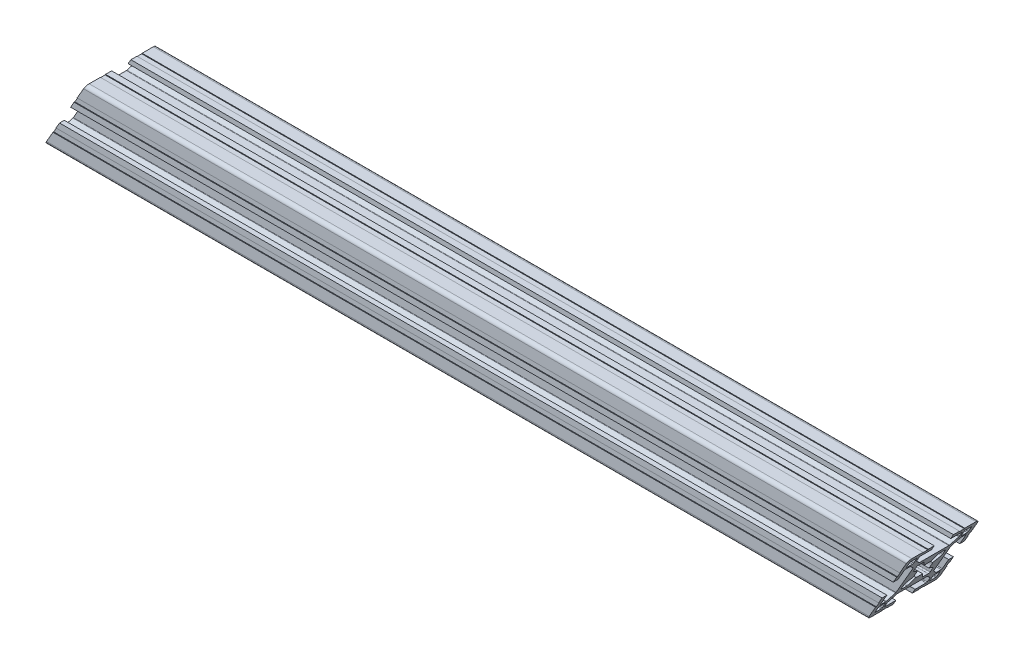
SolidWorks part; units mm, degrees
material "6063-T5"
ref_plane "Plano frontal" through (0, 0, 0) normal (0, 0, 1) x (1, 0, 0)
ref_plane "Plano superior" through (0, 0, 0) normal (0, 1, 0) x (1, 0, 0)
ref_plane "Plano direito" through (0, 0, 0) normal (1, 0, 0) x (0, 0, -1)
sketch "Esboço1" plane through (0, 0, 0) normal (0, 0, 1) x (1, 0, 0)
  line L0 (0, 0) -> (363.73, 0)
  dimension "D1" = 363.73
other "Quadrado PF30-11 - PERFIL 3030 CENTRO M8(1)"
ref_plane "Plano1" through (0, 0, 0) normal (1, 0, 0) x (0, 1, 0)
sketch "Sketch1" plane through (0, 0, 0) normal (1, 0, 0) x (0, 1, 0)
  line L0 (-6.1, -3.4254) -> (-6.1, -5.6)
  line L1 (-5.6, -6.1) -> (-3.4254, -6.1)
  line L2 (3.4254, -6.1) -> (5.6, -6.1)
  line L3 (6.1, -5.6) -> (6.1, -3.4254)
  line L4 (6.1, 3.4254) -> (6.1, 5.6)
  line L5 (5.6, 6.1) -> (3.4254, 6.1)
  line L6 (-3.4254, 6.1) -> (-5.6, 6.1)
  line L7 (-6.1, 5.6) -> (-6.1, 3.4254)
  line L8 (15, 6.6) -> (14.7, 6.6)
  line L9 (5.85, -2.9924) -> (3.097, -1.403)
  line L10 (10, 12.7) -> (10, 10.3)
  line L11 (13, -12.7) -> (13, -10.3)
  line L12 (-10.3, -10) -> (-12.7, -10)
  line L13 (-13, 12.7) -> (-13, 10.3)
  line L14 (3.097, 1.403) -> (5.85, 2.9924)
  line L15 (2.9924, 5.85) -> (1.403, 3.097)
  line L16 (-1.403, 3.097) -> (-2.9924, 5.85)
  line L17 (-5.85, 2.9924) -> (-3.097, 1.403)
  line L18 (-3.097, -1.403) -> (-5.85, -2.9924)
  line L19 (-2.9924, -5.85) -> (-1.403, -3.097)
  line L20 (1.403, -3.097) -> (2.9924, -5.85)
  line L21 (10.3, 10) -> (12.7, 10)
  line L22 (13, 10.3) -> (13, 12.7)
  line L23 (12.7, 13) -> (10.3, 13)
  line L24 (12.7, -10) -> (10.3, -10)
  line L25 (10, -10.3) -> (10, -12.7)
  line L26 (10.3, -13) -> (12.7, -13)
  line L27 (-13, -10.3) -> (-13, -12.7)
  line L28 (-12.7, -13) -> (-10.3, -13)
  line L29 (-10, -12.7) -> (-10, -10.3)
  line L30 (-12.7, 10) -> (-10.3, 10)
  line L31 (-10, 10.3) -> (-10, 12.7)
  line L32 (-10.3, 13) -> (-12.7, 13)
  line L33 (15, 4.05) -> (15, 6.6)
  line L34 (13, 4.05) -> (15, 4.05)
  line L35 (13, 8.7) -> (13, 4.05)
  line L36 (10.6799, 9) -> (12.7, 9)
  line L37 (7.9879, 6.4322) -> (10.4678, 8.9121)
  line L38 (7.9, -6.2201) -> (7.9, 6.2201)
  line L39 (10.4678, -8.9121) -> (7.9879, -6.4322)
  line L40 (12.7, -9) -> (10.6799, -9)
  line L41 (13, -4.05) -> (13, -8.7)
  line L42 (15, -4.05) -> (13, -4.05)
  line L43 (15, -6.6) -> (15, -4.05)
  line L44 (14.7, -6.6) -> (15, -6.6)
  line L45 (14.7, -8.8) -> (14.7, -6.6)
  line L46 (15, -8.8) -> (14.7, -8.8)
  line L47 (15, -13.5) -> (15, -8.8)
  line L48 (8.8, -15) -> (13.5, -15)
  line L49 (8.8, -14.7) -> (8.8, -15)
  line L50 (6.6, -14.7) -> (8.8, -14.7)
  line L51 (6.6, -15) -> (6.6, -14.7)
  line L52 (4.05, -15) -> (6.6, -15)
  line L53 (4.05, -13) -> (4.05, -15)
  line L54 (8.7, -13) -> (4.05, -13)
  line L55 (9, -10.6799) -> (9, -12.7)
  line L56 (6.4322, -7.9879) -> (8.9121, -10.4678)
  line L57 (-6.2201, -7.9) -> (6.2201, -7.9)
  line L58 (-8.9121, -10.4678) -> (-6.4322, -7.9879)
  line L59 (-9, -12.7) -> (-9, -10.6799)
  line L60 (-4.05, -13) -> (-8.7, -13)
  line L61 (-4.05, -15) -> (-4.05, -13)
  line L62 (-6.6, -15) -> (-4.05, -15)
  line L63 (-6.6, -14.7) -> (-6.6, -15)
  line L64 (-8.8, -14.7) -> (-6.6, -14.7)
  line L65 (-8.8, -15) -> (-8.8, -14.7)
  line L66 (-13.5, -15) -> (-8.8, -15)
  line L67 (-15, -8.8) -> (-15, -13.5)
  line L68 (-14.7, -8.8) -> (-15, -8.8)
  line L69 (-14.7, -6.6) -> (-14.7, -8.8)
  line L70 (-15, -6.6) -> (-14.7, -6.6)
  line L71 (-15, -4.05) -> (-15, -6.6)
  line L72 (-13, -4.05) -> (-15, -4.05)
  line L73 (-13, -8.7) -> (-13, -4.05)
  line L74 (-10.6799, -9) -> (-12.7, -9)
  line L75 (-7.9879, -6.4322) -> (-10.4678, -8.9121)
  line L76 (-7.9, 6.2201) -> (-7.9, -6.2201)
  line L77 (-10.4678, 8.9121) -> (-7.9879, 6.4322)
  line L78 (-12.7, 9) -> (-10.6799, 9)
  line L79 (-13, 4.05) -> (-13, 8.7)
  line L80 (-15, 4.05) -> (-13, 4.05)
  line L81 (-15, 6.6) -> (-15, 4.05)
  line L82 (-14.7, 6.6) -> (-15, 6.6)
  line L83 (-14.7, 8.8) -> (-14.7, 6.6)
  line L84 (-15, 8.8) -> (-14.7, 8.8)
  line L85 (-15, 13.5) -> (-15, 8.8)
  line L86 (-8.8, 15) -> (-13.5, 15)
  line L87 (-8.8, 14.7) -> (-8.8, 15)
  line L88 (-6.6, 14.7) -> (-8.8, 14.7)
  line L89 (-6.6, 15) -> (-6.6, 14.7)
  line L90 (-4.05, 15) -> (-6.6, 15)
  line L91 (-4.05, 13) -> (-4.05, 15)
  line L92 (-8.7, 13) -> (-4.05, 13)
  line L93 (-9, 10.6799) -> (-9, 12.7)
  line L94 (-6.4322, 7.9879) -> (-8.9121, 10.4678)
  line L95 (6.2201, 7.9) -> (-6.2201, 7.9)
  line L96 (8.9121, 10.4678) -> (6.4322, 7.9879)
  line L97 (9, 12.7) -> (9, 10.6799)
  line L98 (4.05, 13) -> (8.7, 13)
  line L99 (4.05, 15) -> (4.05, 13)
  line L100 (6.6, 15) -> (4.05, 15)
  line L101 (6.6, 14.7) -> (6.6, 15)
  line L102 (8.8, 14.7) -> (6.6, 14.7)
  line L103 (8.8, 15) -> (8.8, 14.7)
  line L104 (13.5, 15) -> (8.8, 15)
  line L105 (15, 8.8) -> (15, 13.5)
  line L106 (14.7, 8.8) -> (15, 8.8)
  line L107 (14.7, 6.6) -> (14.7, 8.8)
  arc A0 (-5.85, -2.9924) -> (-6.1, -3.4254) centre (-5.6, -3.4254) ccw
  arc A1 (-6.1, -5.6) -> (-5.6, -6.1) centre (-5.6, -5.6) ccw
  arc A2 (-3.4254, -6.1) -> (-2.9924, -5.85) centre (-3.4254, -5.6) ccw
  arc A3 (2.9924, -5.85) -> (3.4254, -6.1) centre (3.4254, -5.6) ccw
  arc A4 (5.6, -6.1) -> (6.1, -5.6) centre (5.6, -5.6) ccw
  arc A5 (6.1, -3.4254) -> (5.85, -2.9924) centre (5.6, -3.4254) ccw
  arc A6 (5.85, 2.9924) -> (6.1, 3.4254) centre (5.6, 3.4254) ccw
  arc A7 (6.1, 5.6) -> (5.6, 6.1) centre (5.6, 5.6) ccw
  arc A8 (3.4254, 6.1) -> (2.9924, 5.85) centre (3.4254, 5.6) ccw
  arc A9 (-2.9924, 5.85) -> (-3.4254, 6.1) centre (-3.4254, 5.6) ccw
  arc A10 (-5.6, 6.1) -> (-6.1, 5.6) centre (-5.6, 5.6) ccw
  arc A11 (-6.1, 3.4254) -> (-5.85, 2.9924) centre (-5.6, 3.4254) ccw
  arc A12 (3.097, -1.403) -> (3.097, 1.403) centre (0, 0) ccw
  arc A13 (1.403, 3.097) -> (-1.403, 3.097) centre (0, 0) ccw
  arc A14 (-3.097, 1.403) -> (-3.097, -1.403) centre (0, 0) ccw
  arc A15 (-1.403, -3.097) -> (1.403, -3.097) centre (0, 0) ccw
  arc A16 (10, 10.3) -> (10.3, 10) centre (10.3, 10.3) ccw
  arc A17 (12.7, 10) -> (13, 10.3) centre (12.7, 10.3) ccw
  arc A18 (13, 12.7) -> (12.7, 13) centre (12.7, 12.7) ccw
  arc A19 (10.3, 13) -> (10, 12.7) centre (10.3, 12.7) ccw
  arc A20 (13, -10.3) -> (12.7, -10) centre (12.7, -10.3) ccw
  arc A21 (10.3, -10) -> (10, -10.3) centre (10.3, -10.3) ccw
  arc A22 (10, -12.7) -> (10.3, -13) centre (10.3, -12.7) ccw
  arc A23 (12.7, -13) -> (13, -12.7) centre (12.7, -12.7) ccw
  arc A24 (-12.7, -10) -> (-13, -10.3) centre (-12.7, -10.3) ccw
  arc A25 (-13, -12.7) -> (-12.7, -13) centre (-12.7, -12.7) ccw
  arc A26 (-10.3, -13) -> (-10, -12.7) centre (-10.3, -12.7) ccw
  arc A27 (-10, -10.3) -> (-10.3, -10) centre (-10.3, -10.3) ccw
  arc A28 (-13, 10.3) -> (-12.7, 10) centre (-12.7, 10.3) ccw
  arc A29 (-10.3, 10) -> (-10, 10.3) centre (-10.3, 10.3) ccw
  arc A30 (-10, 12.7) -> (-10.3, 13) centre (-10.3, 12.7) ccw
  arc A31 (-12.7, 13) -> (-13, 12.7) centre (-12.7, 12.7) ccw
  arc A32 (13, 8.7) -> (12.7, 9) centre (12.7, 8.7) ccw
  arc A33 (10.6799, 9) -> (10.4678, 8.9121) centre (10.6799, 8.7) ccw
  arc A34 (7.9879, 6.4322) -> (7.9, 6.2201) centre (8.2, 6.2201) ccw
  arc A35 (7.9, -6.2201) -> (7.9879, -6.4322) centre (8.2, -6.2201) ccw
  arc A36 (10.4678, -8.9121) -> (10.6799, -9) centre (10.6799, -8.7) ccw
  arc A37 (12.7, -9) -> (13, -8.7) centre (12.7, -8.7) ccw
  arc A38 (13.5, -15) -> (15, -13.5) centre (13.5, -13.5) ccw
  arc A39 (8.7, -13) -> (9, -12.7) centre (8.7, -12.7) ccw
  arc A40 (9, -10.6799) -> (8.9121, -10.4678) centre (8.7, -10.6799) ccw
  arc A41 (6.4322, -7.9879) -> (6.2201, -7.9) centre (6.2201, -8.2) ccw
  arc A42 (-6.2201, -7.9) -> (-6.4322, -7.9879) centre (-6.2201, -8.2) ccw
  arc A43 (-8.9121, -10.4678) -> (-9, -10.6799) centre (-8.7, -10.6799) ccw
  arc A44 (-9, -12.7) -> (-8.7, -13) centre (-8.7, -12.7) ccw
  arc A45 (-15, -13.5) -> (-13.5, -15) centre (-13.5, -13.5) ccw
  arc A46 (-13, -8.7) -> (-12.7, -9) centre (-12.7, -8.7) ccw
  arc A47 (-10.6799, -9) -> (-10.4678, -8.9121) centre (-10.6799, -8.7) ccw
  arc A48 (-7.9879, -6.4322) -> (-7.9, -6.2201) centre (-8.2, -6.2201) ccw
  arc A49 (-7.9, 6.2201) -> (-7.9879, 6.4322) centre (-8.2, 6.2201) ccw
  arc A50 (-10.4678, 8.9121) -> (-10.6799, 9) centre (-10.6799, 8.7) ccw
  arc A51 (-12.7, 9) -> (-13, 8.7) centre (-12.7, 8.7) ccw
  arc A52 (-13.5, 15) -> (-15, 13.5) centre (-13.5, 13.5) ccw
  arc A53 (-8.7, 13) -> (-9, 12.7) centre (-8.7, 12.7) ccw
  arc A54 (-9, 10.6799) -> (-8.9121, 10.4678) centre (-8.7, 10.6799) ccw
  arc A55 (-6.4322, 7.9879) -> (-6.2201, 7.9) centre (-6.2201, 8.2) ccw
  arc A56 (6.2201, 7.9) -> (6.4322, 7.9879) centre (6.2201, 8.2) ccw
  arc A57 (8.9121, 10.4678) -> (9, 10.6799) centre (8.7, 10.6799) ccw
  arc A58 (9, 12.7) -> (8.7, 13) centre (8.7, 12.7) ccw
  arc A59 (15, 13.5) -> (13.5, 15) centre (13.5, 13.5) ccw
  point P1 (0, 0)
  point P2 (0, 0)
  point P3 (-15, -15)
  point P4 (0, -15)
  point P5 (-15, 0)
  point P230 (-15, 15)
  point P231 (0, 15)
  point P232 (15, 15)
  point P233 (15, 0)
  point P234 (15, -15)
  point P235 (0, -15)
  point P236 (-15, -15)
  point P237 (-15, 0)
  point P238 (0, 0)
  point P239 (0, 0)
sketch "Esboço2" plane through (0, 0, 0) normal (0, 0, 1) x (1, 0, 0)
  line L0 (363.73, 15) -> (346.4095, -15)
  line L1 (363.73, -15) -> (0, -15) construction
  line L2 (346.4095, -15) -> (363.73, -15)
  line L3 (363.73, -15) -> (363.73, 15)
  line L4 (0, -15) -> (0, 15)
  line L5 (0, 15) -> (17.3205, 15)
  line L6 (363.73, 15) -> (0, 15) construction
  line L7 (17.3205, 15) -> (0, -15)
  dimension "D1" = 60
  dimension "D2" = 60
extrude "Corte-extrusão1" cut sketch "Esboço2" against normal through all both and the other way through all
